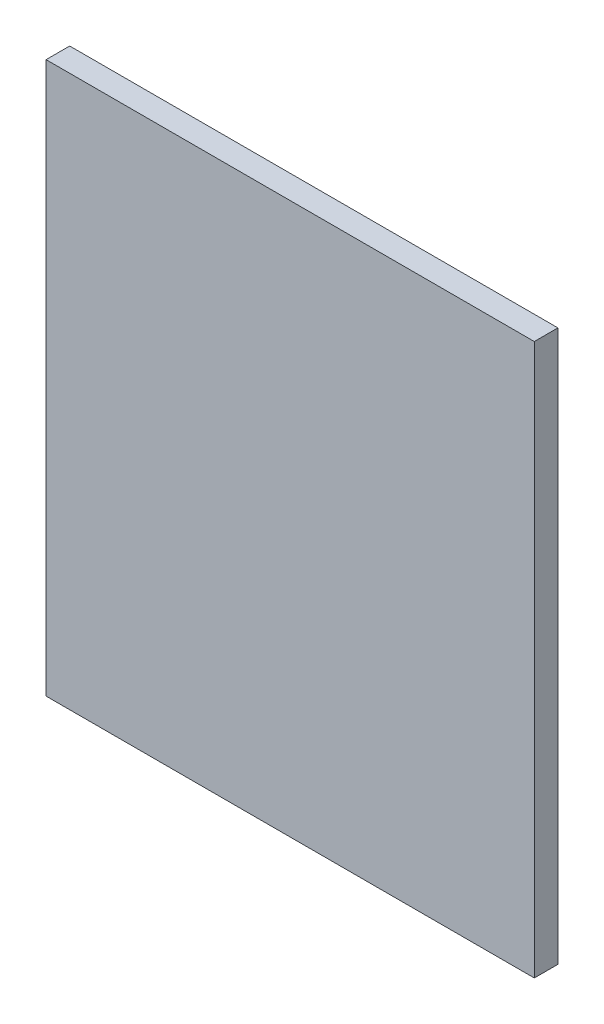
SolidWorks part; units mm, degrees
ref_plane "Plan de face" through (0, 0, 0) normal (0, 0, 1) x (1, 0, 0)
ref_plane "Plan de dessus" through (0, 0, 0) normal (0, 1, 0) x (1, 0, 0)
ref_plane "Plan de droite" through (0, 0, 0) normal (1, 0, 0) x (0, 0, -1)
sketch "Esquisse1" plane through (0, 0, 0) normal (0, 0, 1) x (1, 0, 0)
  line L1 (-155, 175) -> (155, 175)
  line L2 (-155, 175) -> (-155, -175)
  line L3 (-155, -175) -> (155, -175)
  line L4 (155, 175) -> (155, -175)
  line L5 (-155, 175) -> (155, -175) construction
  line L6 (-155, -175) -> (155, 175) construction
  point P0 (0, 0)
  dimension "D1" = 310
  dimension "D2" = 350
extrude "Boss.-Extru.1" add sketch "Esquisse1" along normal blind 15
